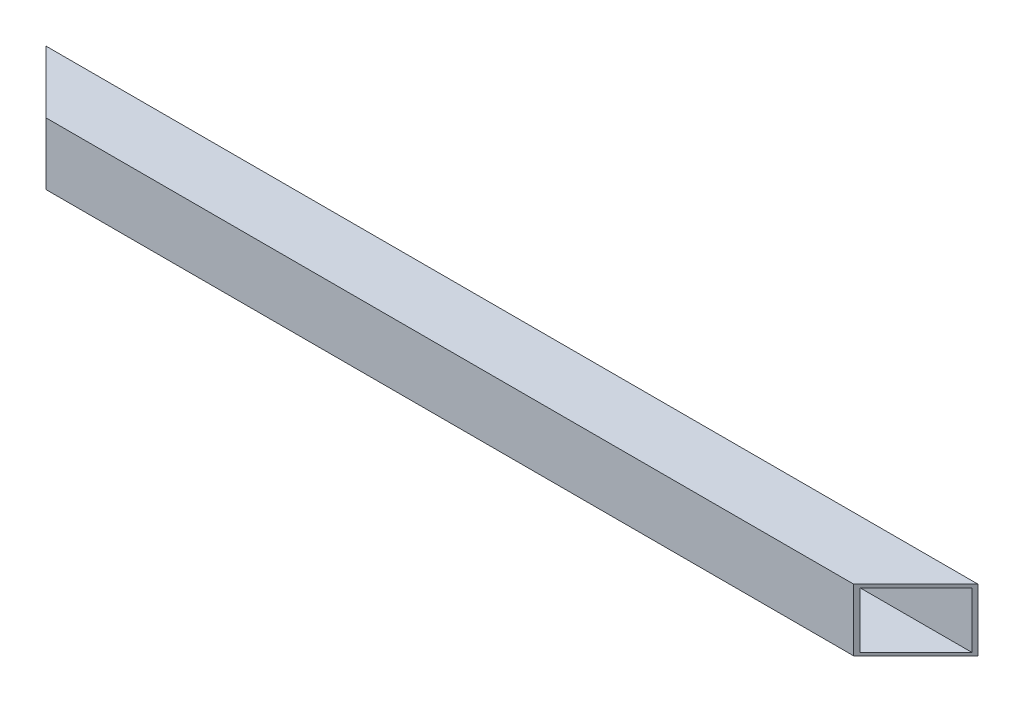
SolidWorks part; units mm, degrees
ref_plane "Alzado" through (0, 0, 0) normal (0, 0, 1) x (1, 0, 0)
ref_plane "Planta" through (0, 0, 0) normal (0, 1, 0) x (1, 0, 0)
ref_plane "Vista lateral" through (0, 0, 0) normal (1, 0, 0) x (0, 0, -1)
sketch "Croquis1" plane through (0, 0, 0) normal (1, 0, 0) x (0, 0, -1)
  line L1 (-20, -20) -> (20, -20)
  line L2 (-20, -20) -> (-20, 20)
  line L3 (-20, 20) -> (20, 20)
  line L4 (20, -20) -> (20, 20)
  line L5 (-20, -20) -> (20, 20) construction
  line L6 (-20, 20) -> (20, -20) construction
  line L7 (-18, -18) -> (18, -18)
  line L8 (-18, -18) -> (-18, 18)
  line L9 (-18, 18) -> (18, 18)
  line L10 (18, -18) -> (18, 18)
  line L11 (-18, -18) -> (18, 18) construction
  line L12 (-18, 18) -> (18, -18) construction
  point P0 (0, 0)
  point P6 (0, 0)
  dimension "D1" = 2
  dimension "D2" = 2
  dimension "D3" = 40
extrude "Saliente-Extruir1" add sketch "Croquis1" along normal blind 600
sketch "Croquis2" plane through (0, 20, 0) normal (0, 1, 0) x (1, 0, 0)
  line L0 (0, 20) -> (0, -20)
  line L2 (0, -20) -> (40, -20)
  line L3 (600, 20) -> (0, 20) construction
  line L4 (600, -20) -> (0, -20) construction
  line L5 (300, 20) -> (300, 80.8862) construction
  line L6 (40, -20) -> (0, 20)
  line L7 (560, -20) -> (600, 20)
  line L8 (600, -20) -> (560, -20)
  line L9 (600, 20) -> (600, -20)
  dimension "D1" = 40
extrude "Cortar-Extruir2" cut sketch "Croquis2" against normal through all
